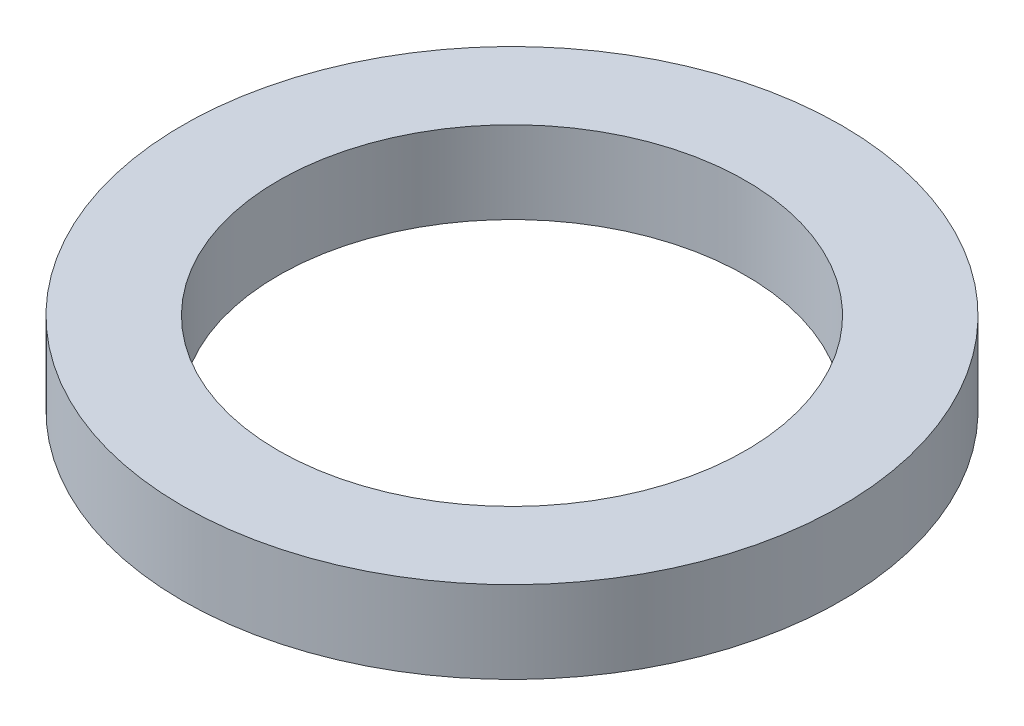
SolidWorks part; units mm, degrees
material "G10 Fiberglass"
ref_plane "Front Plane" through (0, 0, 0) normal (0, 0, 1) x (1, 0, 0)
ref_plane "Top Plane" through (0, 0, 0) normal (0, 1, 0) x (1, 0, 0)
ref_plane "Right Plane" through (0, 0, 0) normal (1, 0, 0) x (0, 0, -1)
sketch "Sketch1" plane through (0, 0, 0) normal (0, 0, 1) x (1, 0, 0)
  line L0 (0, 22.7096) -> (0, -29.6046) construction
  line L2 (27.1145, -12.7) -> (38.227, -12.7)
  line L3 (27.1145, -12.7) -> (27.1145, -3.175)
  line L4 (27.1145, -3.175) -> (38.227, -3.175)
  line L5 (38.227, -12.7) -> (38.227, -3.175)
  dimension "D1" = 38.227
  dimension "D2" = 9.525
  dimension "D3" = 27.1145
  dimension "D4" = 12.7
revolve "Revolve1" add sketch "Sketch1" angle 360 about L0
